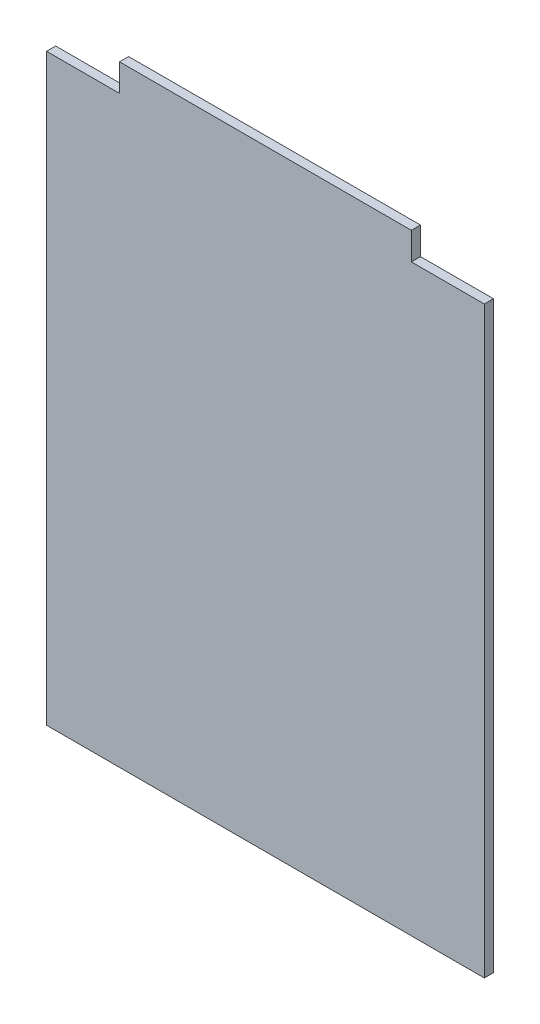
SolidWorks part; units mm, degrees
ref_plane "Plan de face" through (0, 0, 0) normal (0, 0, 1) x (1, 0, 0)
ref_plane "Plan de dessus" through (0, 0, 0) normal (0, 1, 0) x (1, 0, 0)
ref_plane "Plan de droite" through (0, 0, 0) normal (1, 0, 0) x (0, 0, -1)
sketch "Esquisse1" plane through (0, 0, 0) normal (0, 0, 1) x (1, 0, 0)
  line L1 (-290, 335) -> (190, 335)
  line L2 (-290, 335) -> (-290, -335)
  line L3 (-290, -335) -> (190, -335)
  line L4 (190, 335) -> (190, -335)
  dimension "D1" = 480
  dimension "D2" = 670
  dimension "D3" = 335
  dimension "D4" = 190
extrude "Boss.-Extru.1" add sketch "Esquisse1" along normal blind 10
sketch "Esquisse2" plane through (0, 0, 0) normal (0, 0, -1) x (-1, 0, 0)
  line L1 (-190, 335) -> (-110, 335)
  line L2 (-190, 335) -> (-190, 305)
  line L3 (-190, 305) -> (-110, 305)
  line L4 (-110, 335) -> (-110, 305)
  line L5 (290, 335) -> (210, 335)
  line L6 (290, 335) -> (290, 305)
  line L7 (290, 305) -> (210, 305)
  line L8 (210, 335) -> (210, 305)
  dimension "D1" = 30
  dimension "D2" = 30
  dimension "D3" = 80
  dimension "D4" = 80
extrude "Enlèv. mat.-Extru.1" cut sketch "Esquisse2" against normal through all
